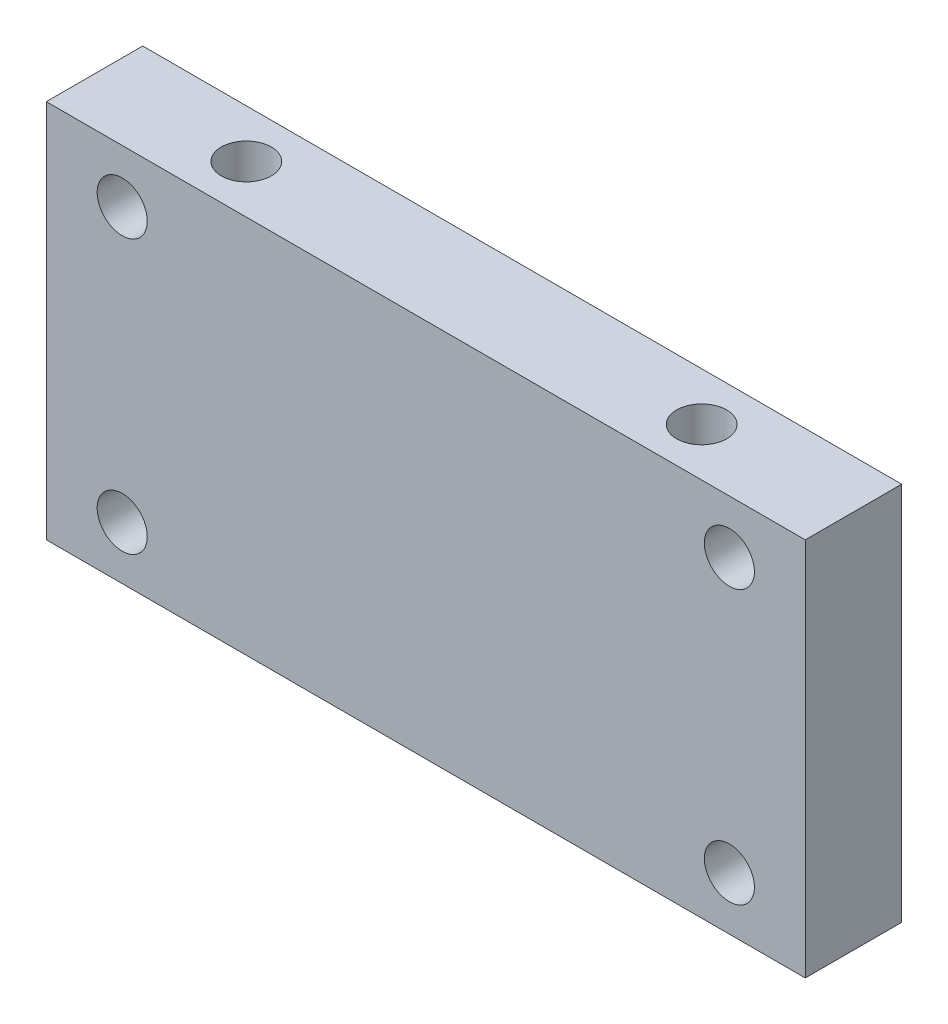
SolidWorks part; units mm, degrees
material "1060 Alloy"
ref_plane "Front Plane" through (0, 0, 0) normal (0, 0, 1) x (1, 0, 0)
ref_plane "Top Plane" through (0, 0, 0) normal (0, 1, 0) x (1, 0, 0)
ref_plane "Right Plane" through (0, 0, 0) normal (1, 0, 0) x (0, 0, -1)
sketch "Sketch1" plane through (0, 0, 0) normal (0, 1, 0) x (1, 0, 0)
  line L1 (0, 0) -> (50, 0)
  line L2 (0, 0) -> (0, 6.35)
  line L3 (0, 6.35) -> (50, 6.35)
  line L4 (50, 0) -> (50, 6.35)
  dimension "D1" = 6.35
  dimension "D2" = 50
extrude "Boss-Extrude1" add sketch "Sketch1" along normal blind 25
sketch "Sketch2" plane through (0, 25, 0) normal (0, 1, 0) x (1, 0, 0)
  line L0 (50, 3.175) -> (0, 3.175) construction
  line L1 (50, 0) -> (50, 6.35) construction
  line L2 (0, 6.35) -> (0, 0) construction
  line L3 (25, 0) -> (25, 6.35) construction
  line L4 (0, 0) -> (50, 0) construction
  line L5 (50, 6.35) -> (0, 6.35) construction
  point P6 (40, 3.175)
  point P13 (10, 3.175)
  dimension "D1" = 15
hole_wizard "M4x0.7 Tapped Hole1" positions "3DSketch1" profile "Sketch3" tap size "M4x0.7" standard "ANSI Metric"
sketch3d "3DSketch1"
  point P0 (40, 25, -3.175)
  point P3 (10, 25, -3.175)
sketch "Sketch3" plane through (40, 25, -3.175) normal (1, 0, 0) x (0, 0, 1)
  line L0 (0, 0) -> (0, 11.0914)
  line L1 (0, 11.0914) -> (1.65, 10.1)
  line L2 (1.65, 10.1) -> (1.65, 0)
  line L5 (1.65, 0) -> (0, 0)
  line L10 (0, 11.0914) -> (-1.65, 10.1) construction
  line L11 (0, -6.35) -> (0, 107.95) construction
  dimension "Tap Drill Dia." = 3.3
  dimension "Tap Drill Depth" = 10.1
  dimension "Drill Angle" = 118
sketch "Sketch4" plane through (0, 0, 0) normal (0, 0, 1) x (1, 0, 0)
  line L0 (0, 12.5) -> (50, 12.5) construction
  line L1 (0, 25) -> (0, 0) construction
  line L2 (50, 25) -> (50, 0) construction
  line L3 (25, 25) -> (25, 0) construction
  line L4 (50, 25) -> (0, 25) construction
  line L5 (0, 0) -> (50, 0) construction
  point P12 (5, 21.5)
  point P14 (45, 21.5)
  point P16 (45, 3.5)
  point P17 (5, 3.5)
  dimension "D1" = 20
  dimension "D2" = 9
hole_wizard "M4x0.7 Tapped Hole2" positions "3DSketch2" profile "Sketch5" tap size "M4x0.7" standard "ANSI Metric"
sketch3d "3DSketch2"
  point P0 (5, 21.5, 0)
  point P3 (45, 21.5, 0)
  point P6 (45, 3.5, 0)
  point P9 (5, 3.5, 0)
sketch "Sketch5" plane through (5, 21.5, 0) normal (1, 0, 0) x (0, -1, 0)
  line L0 (0, 0) -> (0, 11.0914)
  line L1 (0, 11.0914) -> (1.65, 10.1)
  line L2 (1.65, 10.1) -> (1.65, 0)
  line L5 (1.65, 0) -> (0, 0)
  line L10 (0, 11.0914) -> (-1.65, 10.1) construction
  line L11 (0, -6.35) -> (0, 107.95) construction
  dimension "Tap Drill Dia." = 3.3
  dimension "Tap Drill Depth" = 10.1
  dimension "Drill Angle" = 118
